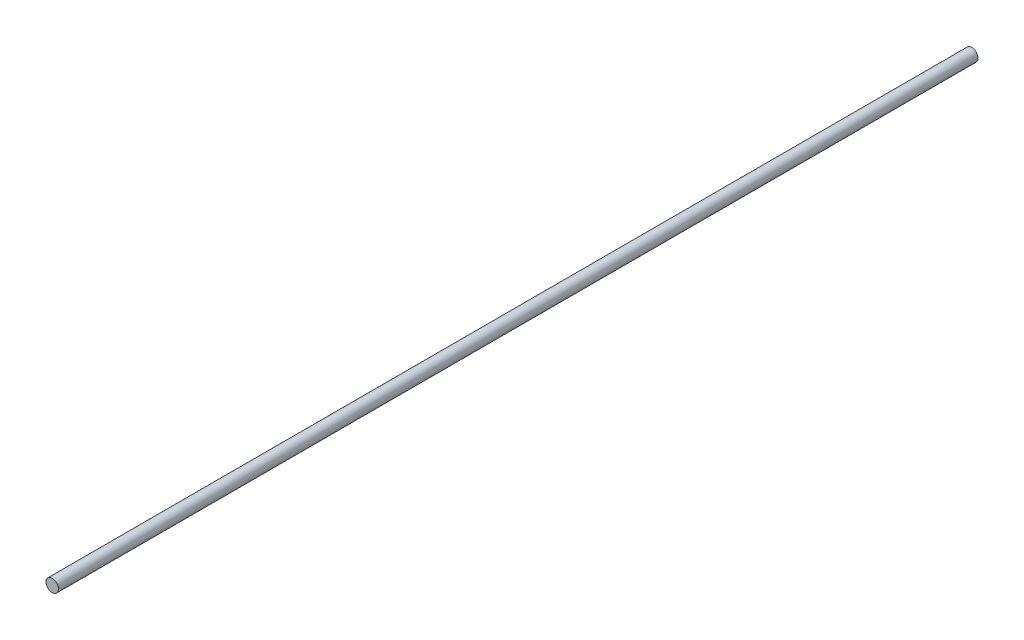
SolidWorks part; units mm, degrees
ref_plane "Plan de face" through (0, 0, 0) normal (0, 0, 1) x (1, 0, 0)
ref_plane "Plan de dessus" through (0, 0, 0) normal (0, 1, 0) x (1, 0, 0)
ref_plane "Plan de droite" through (0, 0, 0) normal (1, 0, 0) x (0, 0, -1)
sketch "Esquisse1" plane through (0, 0, 0) normal (0, 0, 1) x (1, 0, 0)
  circle A0 centre (0, 0) radius 4
  dimension "D1" = 8
extrude "Boss.-Extru.1" add sketch "Esquisse1" along normal blind 590
